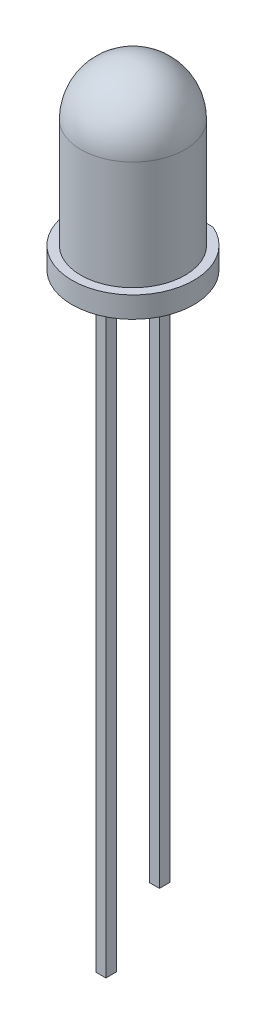
SolidWorks part; units mm, degrees
ref_plane "Front" through (0, 0, 0) normal (0, 0, 1) x (1, 0, 0)
ref_plane "Top" through (0, 0, 0) normal (0, 1, 0) x (1, 0, 0)
ref_plane "Right" through (0, 0, 0) normal (1, 0, 0) x (0, 0, -1)
sketch "草图1" plane through (0, 0, 0) normal (0, 1, 0) x (1, 0, 0)
  line L0 (-1.15, 2.635) -> (1.15, 2.635)
  line L1 (0, 7.3673) -> (0, -7.417) construction
  arc A0 (-1.15, 2.635) -> (1.15, 2.635) centre (0, 0) ccw
  point P7 (0, -2.875)
  dimension "D1" = 5.75
  dimension "D2" = 5.51
extrude "凸台-拉伸1" add sketch "草图1" along normal blind 1
sketch "草图2" plane through (0, 1, 0) normal (0, 1, 0) x (1, 0, 0)
  circle A0 centre (0, 0) radius 2.46
  dimension "D1" = 4.92
extrude "凸台-拉伸2" add sketch "草图2" along normal blind 7.6
sketch "草图3" plane through (0, 0, 0) normal (1, 0, 0) x (0, 0, -1)
  line L0 (-2.46, 6.14) -> (-4.6084, 6.14)
  line L1 (-4.6084, 6.14) -> (-4.6084, 10.2055)
  line L2 (-4.6084, 10.2055) -> (0, 10.2055)
  line L3 (0, 10.2055) -> (0, 8.6)
  line L4 (0, 10.969) -> (0, 4.8263) construction
  arc A0 (0, 8.6) -> (-2.46, 6.14) centre (0, 6.14) ccw
revolve "切除-旋转1" cut sketch "草图3" angle 360 about L4
sketch "草图4" plane through (0, 0, 0) normal (0, -1, 0) x (1, 0, 0)
  line L0 (1.15, -2.635) -> (-1.15, -2.635) construction
  line L1 (-0.235, -1.515) -> (0.235, -1.515)
  line L2 (-0.235, -1.515) -> (-0.235, -1.015)
  line L3 (-0.235, -1.015) -> (0.235, -1.015)
  line L4 (0.235, -1.515) -> (0.235, -1.015)
  line L5 (-0.235, -1.515) -> (0.235, -1.015) construction
  line L6 (-0.235, -1.015) -> (0.235, -1.515) construction
  line L7 (0, 3.1233) -> (0, -2.873) construction
  line L8 (-1.5595, 0) -> (1.8117, 0) construction
  line L9 (-0.235, 1.515) -> (0.235, 1.515)
  line L10 (0.235, 1.515) -> (0.235, 1.015)
  line L11 (-0.235, 1.015) -> (0.235, 1.015)
  line L12 (-0.235, 1.515) -> (-0.235, 1.015)
  point P0 (0, -1.265)
  point P12 (0, 0)
  point P13 (0, 0)
  dimension "D1" = 1.62
  dimension "D2" = 0.5
  dimension "D3" = 0.47
extrude "凸台-拉伸3" add sketch "草图4" along normal blind 25.7
sketch "草图5" plane through (0, -25.7, 0) normal (0, -1, 0) x (1, 0, 0)
  line L1 (-0.235, 1.515) -> (0.235, 1.515)
  line L2 (-0.235, 1.515) -> (-0.235, 1.015)
  line L3 (-0.235, 1.015) -> (0.235, 1.015)
  line L4 (0.235, 1.515) -> (0.235, 1.015)
extrude "凸台-拉伸4" add sketch "草图5" along normal blind 2.4
